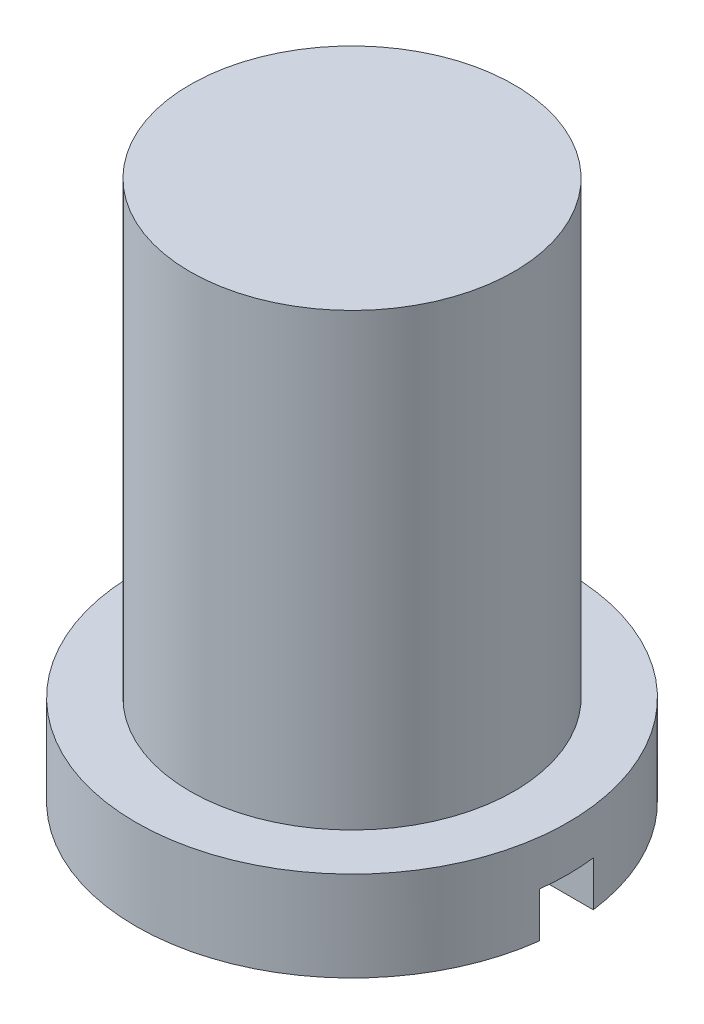
SolidWorks part; units mm, degrees
ref_plane "Plan de face" through (0, 0, 0) normal (0, 0, 1) x (1, 0, 0)
ref_plane "Plan de dessus" through (0, 0, 0) normal (0, 1, 0) x (1, 0, 0)
ref_plane "Plan de droite" through (0, 0, 0) normal (1, 0, 0) x (0, 0, -1)
sketch "Esquisse1" plane through (0, 0, 0) normal (0, 1, 0) x (1, 0, 0)
  circle A0 centre (0, 0) radius 1.8
  circle A1 centre (0, 0) radius 2.4
extrude "Boss.-Extru.1" add sketch "Esquisse1" along normal blind 1 contours A0 | A1 A0
sketch "Esquisse2" plane through (0, 1, 0) normal (0, 1, 0) x (1, 0, 0)
  circle A0 centre (0, 0) radius 1.8
extrude "Boss.-Extru.2" add sketch "Esquisse2" along normal blind 5
sketch "Esquisse3" plane through (0, 0, 0) normal (0, -1, 0) x (1, 0, 0)
  line L0 (-2.4, 0) -> (2.4, 0) construction
  line L7 (2.4, 0) -> (2.4, -0.3)
  line L8 (2.4, -0.3) -> (-2.4, -0.3)
  line L9 (-2.4, -0.3) -> (-2.4, 0)
  line L12 (2.4, 0.2971) -> (2.4, 0)
  line L13 (-2.4, 0) -> (-2.4, 0.2971)
  line L14 (-2.4, 0.2971) -> (2.4, 0.2971)
  circle A1 centre (0, 0) radius 2.4 construction
extrude "Enlèv. mat.-Extru.1" cut sketch "Esquisse3" against normal blind 0.5
